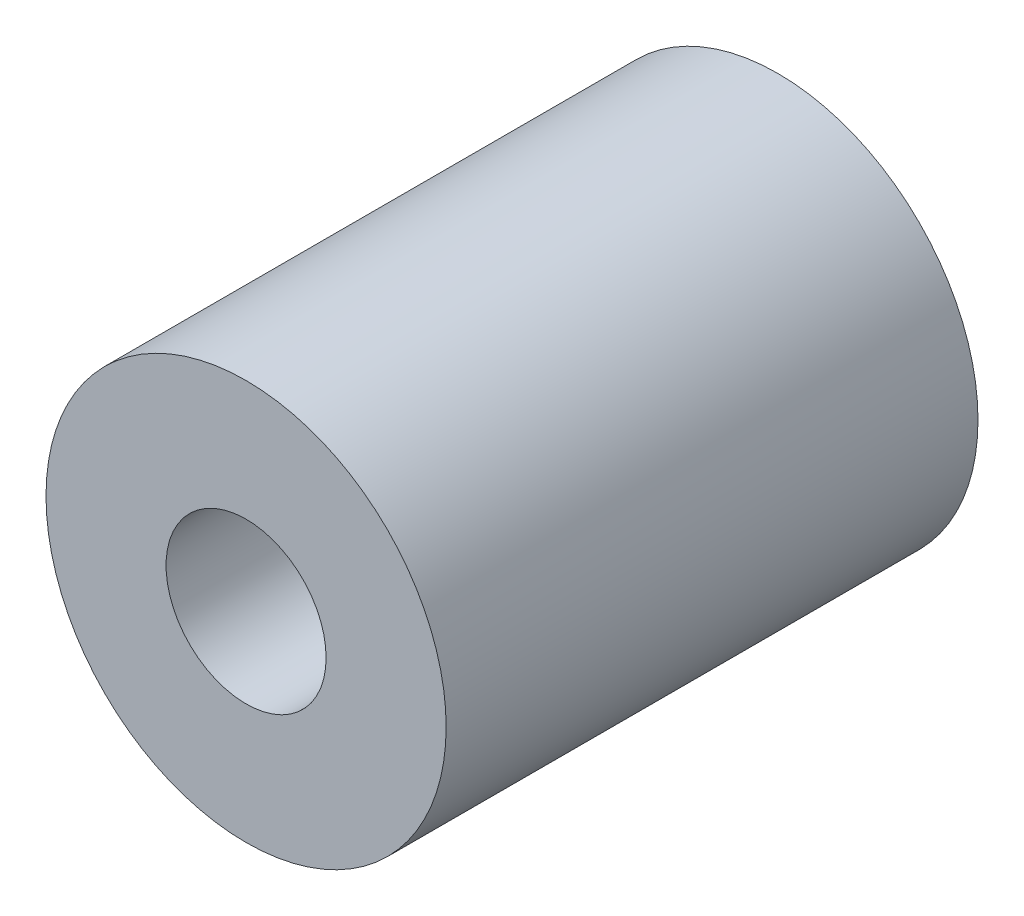
SolidWorks part; units mm, degrees
material "PLA"
ref_plane "Front Plane" through (0, 0, 0) normal (0, 0, 1) x (1, 0, 0)
ref_plane "Top Plane" through (0, 0, 0) normal (0, 1, 0) x (1, 0, 0)
ref_plane "Right Plane" through (0, 0, 0) normal (1, 0, 0) x (0, 0, -1)
sketch "Sketch2" plane through (0, 0, 0) normal (0, 0, 1) x (1, 0, 0)
  circle A0 centre (0, 0) radius 2.75
  dimension "D1" = 5.5
extrude "Boss-Extrude1" add sketch "Sketch2" along normal blind 7.31
hole_wizard "M2 Clearance Hole1" positions "Sketch3" profile "Sketch4" hole size "M2" standard "ANSI Metric" end condition through all
sketch "Sketch3" plane through (0, 0, 7.31) normal (0, 0, 1) x (1, 0, 0)
  point P0 (0, 0)
sketch "Sketch4" plane through (0, 0, 7.31) normal (1, 0, 0) x (0, -1, 0)
  line L0 (0, 0) -> (0, 7.31)
  line L1 (0, 7.31) -> (1.1, 7.31)
  line L2 (1.1, 7.31) -> (1.1, 0)
  line L5 (1.1, 0) -> (0, 0)
  line L11 (0, -6.35) -> (0, 107.95) construction
  dimension "Thru Hole Dia." = 2.2
  dimension "Thru Hole Depth" = 7.31
